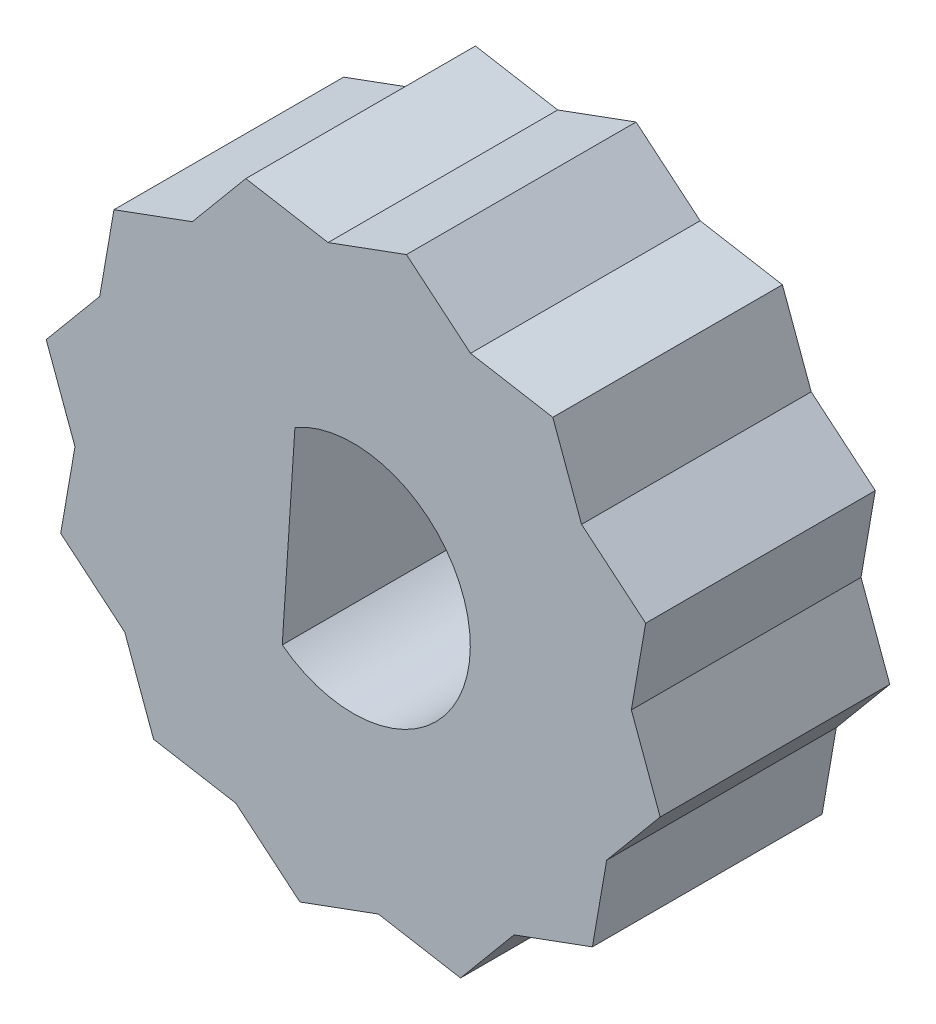
SolidWorks part; units mm, degrees
ref_plane "Front Plane" through (0, 0, 0) normal (0, 0, 1) x (1, 0, 0)
ref_plane "Top Plane" through (0, 0, 0) normal (0, 1, 0) x (1, 0, 0)
ref_plane "Right Plane" through (0, 0, 0) normal (1, 0, 0) x (0, 0, -1)
sketch "Sketch1" plane through (0, 0, 0) normal (0, 0, 1) x (1, 0, 0)
  line L0 (-3.0892, -4.0579) -> (-2.5371, 4.4241)
  line L1 (8.6924, 10.4176) -> (-4.6757, 12.7366)
  line L2 (-4.6757, 12.7366) -> (-13.3681, 2.319)
  line L3 (-13.3681, 2.319) -> (-8.6924, -10.4176)
  line L4 (-8.6924, -10.4176) -> (4.6757, -12.7366)
  line L5 (4.6757, -12.7366) -> (13.3681, -2.319)
  line L6 (13.3681, -2.319) -> (8.6924, 10.4176)
  line L7 (-2.319, -13.3681) -> (10.4176, -8.6924)
  line L8 (10.4176, -8.6924) -> (12.7366, 4.6757)
  line L9 (12.7366, 4.6757) -> (2.319, 13.3681)
  line L10 (2.319, 13.3681) -> (-10.4176, 8.6924)
  line L11 (-10.4176, 8.6924) -> (-12.7366, -4.6757)
  line L12 (-12.7366, -4.6757) -> (-2.319, -13.3681)
  circle A0 centre (0, 0) radius 11.75 construction
  circle A1 centre (0, 0) radius 11.75 construction
  circle A2 centre (0, 0) radius 5.1
  dimension "D2" = 23.5
  dimension "D4" = 23.5
  dimension "D6" = 10.2
  dimension "D10" = 0
  dimension "D1" = 0
  dimension "D3" = 30
  dimension "D5" = 0
  dimension "D7" = 5.1
  dimension "D8" = 5.1
  dimension "D9" = 8.5
extrude "Boss-Extrude2" add sketch "Sketch1" along normal blind 10 contours L10 L11 L2 | L11 L2 L3 | L11 L12 L3 | L12 L3 L4 | L4 L12 L7 | L7 L4 L5 | L7 L8 L5 | L8 L5 L6 | L8 L9 L6 | L9 L6 L1 | L9 L10 L1 | L10 L1 L2 | L0 A2 | L3 L12 L4 L7 L5 L8 L6 L9 L1 L10 L2 L11 A2
